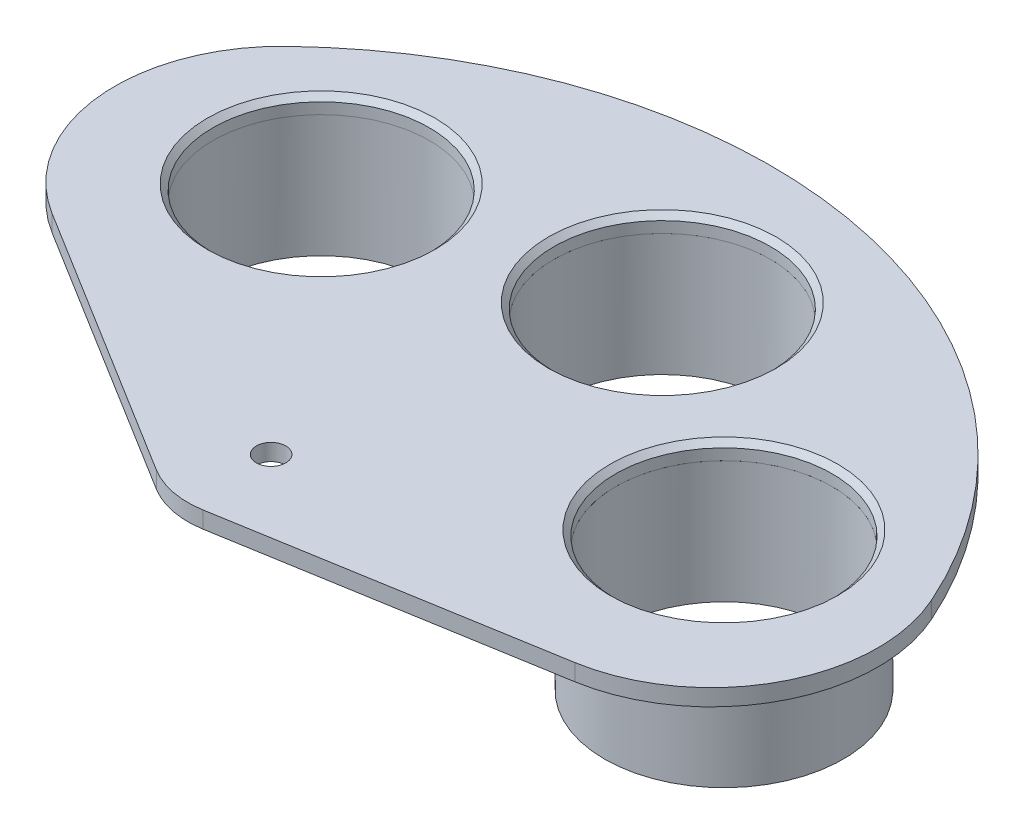
SolidWorks part; units mm, degrees
ref_plane "Front Plane" through (0, 0, 0) normal (0, 0, 1) x (1, 0, 0)
ref_plane "Top Plane" through (0, 0, 0) normal (0, 1, 0) x (1, 0, 0)
ref_plane "Right Plane" through (0, 0, 0) normal (1, 0, 0) x (0, 0, -1)
sketch "Sketch1" plane through (0, 0, 0) normal (0, 1, 0) x (1, 0, 0)
  line L0 (90, 0) -> (0, 0) construction
  line L1 (-83.3323, 33.996) -> (0, 0) construction
  line L2 (-37.6805, 46.6924) -> (11.5479, 58.8782) construction
  line L3 (11.5479, 58.8782) -> (52.5262, 29) construction
  line L4 (0, 0) -> (11.5479, 58.8782) construction
  line L5 (52.5262, 29) -> (52.5262, 0) construction
  line L6 (-37.6805, 46.6924) -> (-48.6348, 19.8409) construction
  line L7 (-57.2826, 17.8524) -> (-7.9015, -12.7501)
  line L8 (2.5, -14.7902) -> (59.7822, -5.1077)
  line L9 (-37.6805, 46.6924) -> (0, 0) construction
  arc A0 (-62.2193, 65.029) -> (82.1733, 36.709) centre (0, 0) cw
  circle A1 centre (-37.6805, 46.6924) radius 19.5
  circle A2 centre (11.5479, 58.8782) radius 19.5
  circle A3 centre (52.5262, 29) radius 19.5
  arc A4 (-37.6805, 46.6924) -> (52.5262, 29) centre (0, 0) cw construction
  arc A5 (-7.9015, -12.7501) -> (2.5, -14.7902) centre (0, 0) ccw
  circle A6 centre (0, 0) radius 1
  arc A7 (-62.2193, 65.029) -> (-57.2826, 17.8524) centre (-41.4795, 43.3526) ccw
  arc A8 (82.1733, 36.709) -> (59.7822, -5.1077) centre (54.7822, 24.4727) cw
  dimension "D1" = 39
  dimension "D6" = 15
  dimension "D7" = 2
  dimension "D8" = 30
  dimension "D2" = 29
  dimension "D3" = 50
  dimension "D4" = 60
  dimension "D5" = 90
extrude "Boss-Extrude1" add sketch "Sketch1" along normal blind 3
sketch "Sketch2" plane through (0, 0, 0) normal (0, 1, 0) x (1, 0, 0)
  circle A1 centre (-37.6805, 46.6924) radius 24
  circle A2 centre (-37.6805, 46.6924) radius 19.5
  circle A3 centre (-37.6805, 46.6924) radius 19.5 construction
  dimension "D1" = 48
extrude "Boss-Extrude2" add sketch "Sketch2" against normal blind 3 separate body
sketch "Sketch3" plane through (0, 0, 0) normal (0, -1, 0) x (-1, 0, 0)
  circle A0 centre (37.6805, 46.6924) radius 19.5
  circle A1 centre (37.6805, 46.6924) radius 21.5
  circle A2 centre (37.6805, 46.6924) radius 19.5 construction
  dimension "D1" = 2
extrude "Boss-Extrude3" add sketch "Sketch3" along normal blind 22
pattern_circular "CirPattern1" count 3 over 100 about axis through (0, 0, 0) along (0, 1, 0) of bodies 103
chamfer "Chamfer1" distance 1 angle 45 3 edges at (52.5262, 3, -9.5) (11.5479, 3, -39.3782) (-37.6805, 3, -27.1924)
hole_wizard "M5 Clearance Hole1" positions "Sketch4" profile "Sketch5" hole size "M5" standard "ISO" end condition through all
sketch "Sketch4" plane through (0, 3, 0) normal (0, 1, 0) x (1, 0, 0)
  point P0 (0, 0)
sketch "Sketch5" plane through (0, 3, 0) normal (1, 0, 0) x (0, 0, 1)
  line L0 (0, 0) -> (0, 25)
  line L1 (0, 25) -> (2.65, 25)
  line L2 (2.65, 25) -> (2.65, 0)
  line L5 (2.65, 0) -> (0, 0)
  line L11 (0, -6.35) -> (0, 107.95) construction
  dimension "Thru Hole Dia." = 5.3
  dimension "Thru Hole Depth" = 25
